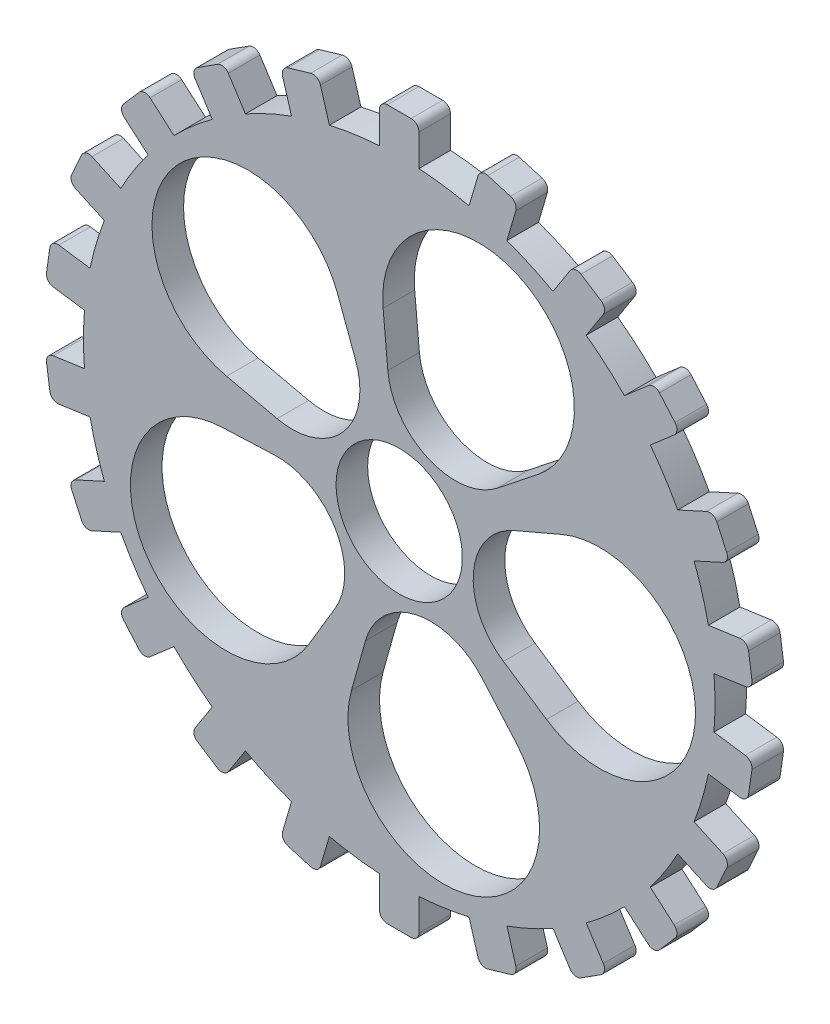
SolidWorks part; units mm, degrees
ref_plane "Front Plane" through (0, 0, 0) normal (0, 0, 1) x (1, 0, 0)
ref_plane "Top Plane" through (0, 0, 0) normal (0, 1, 0) x (1, 0, 0)
ref_plane "Right Plane" through (0, 0, 0) normal (1, 0, 0) x (0, 0, -1)
sketch "Sketch1" plane through (0, 0, 0) normal (0, 0, 1) x (1, 0, 0)
  line L0 (22.4753, 99.0829) -> (25.3377, 108.8314)
  line L2 (-6.35, 101.4014) -> (-6.35, 111.5614)
  line L3 (-3.81, 114.1014) -> (3.81, 114.1014)
  line L4 (6.35, 101.4014) -> (6.35, 111.5614)
  line L5 (28.4904, 110.5529) -> (35.8017, 108.4061)
  line L6 (34.6608, 95.5049) -> (37.5232, 105.2533)
  line L8 (49.4798, 88.7373) -> (54.9727, 97.2845)
  line L9 (58.4827, 98.048) -> (64.893, 93.9283)
  line L10 (60.1637, 81.8712) -> (65.6566, 90.4183)
  line L12 (72.4757, 71.2028) -> (80.1541, 77.8562)
  line L13 (83.737, 77.5999) -> (88.7271, 71.8411)
  line L14 (80.7924, 61.6048) -> (88.4708, 68.2581)
  line L16 (89.6, 47.8998) -> (98.8419, 52.1204)
  line L17 (102.2075, 50.8651) -> (105.373, 43.9337)
  line L18 (94.8758, 36.3475) -> (104.1177, 40.5681)
  line L20 (99.4655, 20.7163) -> (109.5221, 22.1622)
  line L21 (112.3978, 20.0095) -> (113.4822, 12.4671)
  line L22 (101.2729, 8.1456) -> (111.3295, 9.5915)
  line L24 (101.2729, -8.1456) -> (111.3295, -9.5915)
  line L25 (113.4822, -12.4671) -> (112.3978, -20.0095)
  line L26 (99.4655, -20.7163) -> (109.5221, -22.1622)
  line L28 (94.8758, -36.3475) -> (104.1177, -40.5681)
  line L29 (105.373, -43.9337) -> (102.2075, -50.8651)
  line L30 (89.6, -47.8998) -> (98.8419, -52.1204)
  line L32 (80.7924, -61.6048) -> (88.4708, -68.2581)
  line L33 (88.7271, -71.8411) -> (83.737, -77.5999)
  line L34 (72.4757, -71.2028) -> (80.1541, -77.8562)
  line L36 (60.1637, -81.8712) -> (65.6566, -90.4183)
  line L37 (64.893, -93.9283) -> (58.4827, -98.048)
  line L38 (49.4798, -88.7373) -> (54.9727, -97.2845)
  line L40 (34.6608, -95.5049) -> (37.5232, -105.2533)
  line L41 (35.8017, -108.4061) -> (28.4904, -110.5529)
  line L42 (22.4753, -99.0829) -> (25.3377, -108.8314)
  line L44 (6.35, -101.4014) -> (6.35, -111.5614)
  line L45 (3.81, -114.1014) -> (-3.81, -114.1014)
  line L46 (-6.35, -101.4014) -> (-6.35, -111.5614)
  line L48 (-22.4753, -99.0829) -> (-25.3377, -108.8314)
  line L49 (-28.4904, -110.5529) -> (-35.8017, -108.4061)
  line L50 (-34.6608, -95.5049) -> (-37.5232, -105.2533)
  line L52 (-49.4798, -88.7373) -> (-54.9727, -97.2845)
  line L53 (-58.4827, -98.048) -> (-64.893, -93.9283)
  line L54 (-60.1637, -81.8712) -> (-65.6566, -90.4183)
  line L56 (-72.4757, -71.2028) -> (-80.1541, -77.8562)
  line L57 (-83.737, -77.5999) -> (-88.7271, -71.8411)
  line L58 (-80.7924, -61.6048) -> (-88.4708, -68.2581)
  line L60 (-89.6, -47.8998) -> (-98.8419, -52.1204)
  line L61 (-102.2075, -50.8651) -> (-105.373, -43.9337)
  line L62 (-94.8758, -36.3475) -> (-104.1177, -40.5681)
  line L64 (-99.4655, -20.7163) -> (-109.5221, -22.1622)
  line L65 (-112.3978, -20.0095) -> (-113.4822, -12.4671)
  line L66 (-101.2729, -8.1456) -> (-111.3295, -9.5915)
  line L68 (-101.2729, 8.1456) -> (-111.3295, 9.5915)
  line L69 (-113.4822, 12.4671) -> (-112.3978, 20.0095)
  line L70 (-99.4655, 20.7163) -> (-109.5221, 22.1622)
  line L72 (-94.8758, 36.3475) -> (-104.1177, 40.5681)
  line L73 (-105.373, 43.9337) -> (-102.2075, 50.8651)
  line L74 (-89.6, 47.8998) -> (-98.8419, 52.1204)
  line L76 (-80.7924, 61.6048) -> (-88.4708, 68.2581)
  line L77 (-88.7271, 71.8411) -> (-83.737, 77.5999)
  line L78 (-72.4757, 71.2028) -> (-80.1541, 77.8562)
  line L80 (-60.1637, 81.8712) -> (-65.6566, 90.4183)
  line L81 (-64.893, 93.9283) -> (-58.4827, 98.048)
  line L82 (-49.4798, 88.7373) -> (-54.9727, 97.2845)
  line L84 (-34.6608, 95.5049) -> (-37.5232, 105.2533)
  line L85 (-35.8017, 108.4061) -> (-28.4904, 110.5529)
  line L86 (-22.4753, 99.0829) -> (-25.3377, 108.8314)
  arc A0 (-34.6608, 95.5049) -> (-49.4798, 88.7373) centre (0, 0) ccw
  arc A2 (-6.35, 101.4014) -> (-22.4753, 99.0829) centre (0, 0) ccw
  arc A3 (22.4753, 99.0829) -> (6.35, 101.4014) centre (0, 0) ccw
  arc A4 (49.4798, 88.7373) -> (34.6608, 95.5049) centre (0, 0) ccw
  arc A5 (72.4757, 71.2028) -> (60.1637, 81.8712) centre (0, 0) ccw
  arc A6 (89.6, 47.8998) -> (80.7924, 61.6048) centre (0, 0) ccw
  arc A7 (99.4655, 20.7163) -> (94.8758, 36.3475) centre (0, 0) ccw
  arc A8 (101.2729, -8.1456) -> (101.2729, 8.1456) centre (0, 0) ccw
  arc A9 (94.8758, -36.3475) -> (99.4655, -20.7163) centre (0, 0) ccw
  arc A10 (80.7924, -61.6048) -> (89.6, -47.8998) centre (0, 0) ccw
  arc A11 (60.1637, -81.8712) -> (72.4757, -71.2028) centre (0, 0) ccw
  arc A12 (34.6608, -95.5049) -> (49.4798, -88.7373) centre (0, 0) ccw
  arc A13 (-22.4753, -99.0829) -> (-6.35, -101.4014) centre (0, 0) ccw
  arc A14 (6.35, -101.4014) -> (22.4753, -99.0829) centre (0, 0) ccw
  arc A15 (-60.1637, 81.8712) -> (-72.4757, 71.2028) centre (0, 0) ccw
  arc A16 (-80.7924, 61.6048) -> (-89.6, 47.8998) centre (0, 0) ccw
  arc A17 (-94.8758, 36.3475) -> (-99.4655, 20.7163) centre (0, 0) ccw
  arc A18 (-101.2729, 8.1456) -> (-101.2729, -8.1456) centre (0, 0) ccw
  arc A19 (-99.4655, -20.7163) -> (-94.8758, -36.3475) centre (0, 0) ccw
  arc A20 (-89.6, -47.8998) -> (-80.7924, -61.6048) centre (0, 0) ccw
  arc A21 (-72.4757, -71.2028) -> (-60.1637, -81.8712) centre (0, 0) ccw
  arc A22 (-49.4798, -88.7373) -> (-34.6608, -95.5049) centre (0, 0) ccw
  arc A23 (102.2075, 50.8651) -> (98.8419, 52.1204) centre (99.8971, 49.81) ccw
  arc A24 (83.737, 77.5999) -> (80.1541, 77.8562) centre (81.8174, 75.9366) ccw
  arc A25 (58.4827, 98.048) -> (54.9727, 97.2845) centre (57.1095, 95.9112) ccw
  arc A26 (28.4904, 110.5529) -> (25.3377, 108.8314) centre (27.7748, 108.1158) ccw
  arc A27 (-3.81, 114.1014) -> (-6.35, 111.5614) centre (-3.81, 111.5614) ccw
  arc A28 (-25.3377, 108.8314) -> (-28.4904, 110.5529) centre (-27.7748, 108.1158) ccw
  arc A29 (-35.8017, 108.4061) -> (-37.5232, 105.2533) centre (-35.0861, 105.9689) ccw
  arc A30 (-54.9727, 97.2845) -> (-58.4827, 98.048) centre (-57.1095, 95.9112) ccw
  arc A31 (-64.893, 93.9283) -> (-65.6566, 90.4183) centre (-63.5198, 91.7916) ccw
  arc A32 (-83.737, 77.5999) -> (-80.1541, 77.8562) centre (-81.8174, 75.9366) cw
  arc A33 (-88.7271, 71.8411) -> (-88.4708, 68.2581) centre (-86.8075, 70.1778) ccw
  arc A34 (-98.8419, 52.1204) -> (-102.2075, 50.8651) centre (-99.8971, 49.81) ccw
  arc A35 (-105.373, 43.9337) -> (-104.1177, 40.5681) centre (-103.0625, 42.8786) ccw
  arc A36 (-109.5221, 22.1622) -> (-112.3978, 20.0095) centre (-109.8836, 19.6481) ccw
  arc A37 (-113.4822, 12.4671) -> (-111.3295, 9.5915) centre (-110.9681, 12.1056) ccw
  arc A38 (-111.3295, -9.5915) -> (-113.4822, -12.4671) centre (-110.9681, -12.1056) ccw
  arc A39 (-109.5221, -22.1622) -> (-112.3978, -20.0095) centre (-109.8836, -19.6481) cw
  arc A40 (-104.1177, -40.5681) -> (-105.373, -43.9337) centre (-103.0625, -42.8786) ccw
  arc A41 (-102.2075, -50.8651) -> (-98.8419, -52.1204) centre (-99.8971, -49.81) ccw
  arc A42 (-88.4708, -68.2581) -> (-88.7271, -71.8411) centre (-86.8075, -70.1778) ccw
  arc A43 (-83.737, -77.5999) -> (-80.1541, -77.8562) centre (-81.8174, -75.9366) ccw
  arc A44 (-65.6566, -90.4183) -> (-64.893, -93.9283) centre (-63.5198, -91.7916) ccw
  arc A45 (-58.4827, -98.048) -> (-54.9727, -97.2845) centre (-57.1095, -95.9112) ccw
  arc A46 (-37.5232, -105.2533) -> (-35.8017, -108.4061) centre (-35.0861, -105.9689) ccw
  arc A47 (-28.4904, -110.5529) -> (-25.3377, -108.8314) centre (-27.7748, -108.1158) ccw
  arc A48 (-6.35, -111.5614) -> (-3.81, -114.1014) centre (-3.81, -111.5614) ccw
  arc A49 (3.81, -114.1014) -> (6.35, -111.5614) centre (3.81, -111.5614) ccw
  arc A50 (25.3377, -108.8314) -> (28.4904, -110.5529) centre (27.7748, -108.1158) ccw
  arc A51 (35.8017, -108.4061) -> (37.5232, -105.2533) centre (35.0861, -105.9689) ccw
  arc A52 (54.9727, -97.2845) -> (58.4827, -98.048) centre (57.1095, -95.9112) ccw
  arc A53 (64.893, -93.9283) -> (65.6566, -90.4183) centre (63.5198, -91.7916) ccw
  arc A54 (80.1541, -77.8562) -> (83.737, -77.5999) centre (81.8174, -75.9366) ccw
  arc A55 (88.7271, -71.8411) -> (88.4708, -68.2581) centre (86.8075, -70.1778) ccw
  arc A56 (98.8419, -52.1204) -> (102.2075, -50.8651) centre (99.8971, -49.81) ccw
  arc A57 (105.373, -43.9337) -> (104.1177, -40.5681) centre (103.0625, -42.8786) ccw
  arc A58 (109.5221, -22.1622) -> (112.3978, -20.0095) centre (109.8836, -19.6481) ccw
  arc A59 (113.4822, -12.4671) -> (111.3295, -9.5915) centre (110.9681, -12.1056) ccw
  arc A60 (113.4822, 12.4671) -> (111.3295, 9.5915) centre (110.9681, 12.1056) cw
  arc A61 (112.3978, 20.0095) -> (109.5221, 22.1622) centre (109.8836, 19.6481) ccw
  arc A62 (105.373, 43.9337) -> (104.1177, 40.5681) centre (103.0625, 42.8786) cw
  arc A63 (88.7271, 71.8411) -> (88.4708, 68.2581) centre (86.8075, 70.1778) cw
  arc A64 (65.6566, 90.4183) -> (64.893, 93.9283) centre (63.5198, 91.7916) ccw
  arc A65 (35.8017, 108.4061) -> (37.5232, 105.2533) centre (35.0861, 105.9689) cw
  arc A66 (3.81, 114.1014) -> (6.35, 111.5614) centre (3.81, 111.5614) cw
  point P94 (0, 0)
  point P102 (-6.35, 114.1014)
  point P181 (6.35, 114.1014)
  dimension "D1" = 203.2
  dimension "D6" = 2.54
  dimension "D2" = 12.7
  dimension "D3" = 12.7
  dimension "D4" = 22
extrude "Boss-Extrude1" add sketch "Sketch1" along normal blind 10.16 contours A3 L4 A66 L3 A27 L2 A2 L86 A28 L85 A29 L84 A0 L82 A30 L81 A31 L80 A15 L78 A32 L77 A33 L76 A16 L74 A34 L73 A35 L72 A17 L70 A36 L69 A37 L68 A18 L66 A38 L65 A39 L64 A19 L62 A40 L61 A41 L60 A20 L58 A42 L57 A43 L56 A21 L54 A44 L53 A45 L52 A22 L50 A46 L49 A47 L48 A13 L46 A48 L45 A49 L44 A14 L42 A50 L41 A51 L40 A12 L38 A52 L37 A53 L36 A11 L34 A54 L33 A55 L32 A10 L30 A56 L29 A57 L28 A9 L26 A58 L25 A59 L24 A8 L22 A60 L21 A61 L20 A7 L18 A62 L17 A23 L16 A6 L14 A63 L13 A24 L12 A5 L10 A64 L9 A25 L8 A4 L6 A65 L5 A26 L0
sketch "Sketch5" plane through (0, 0, 0) normal (0, 0, -1) x (-1, 0, 0)
  circle A0 centre (0, 0) radius 20.32
extrude "Cut-Extrude1" cut sketch "Sketch5" against normal blind 10.16
sketch "Sketch7" plane through (0, 0, 0) normal (0, 0, -1) x (-1, 0, 0)
  line L0 (56.9012, -2.3358) -> (40.2429, -1.652)
  line L1 (20.6116, -34.6033) -> (29.1436, -48.927)
  line L2 (19.8049, 53.3944) -> (14.0069, 37.7628)
  line L3 (39.279, 8.9098) -> (55.5382, 12.5979)
  line L4 (15.3619, -54.838) -> (10.8646, -38.7838)
  line L5 (-26.5403, -30.2958) -> (-37.5265, -42.8365)
  line L6 (-47.407, -31.556) -> (-33.5282, -22.3177)
  line L7 (-37.0144, 15.8794) -> (-52.3362, 22.4526)
  line L8 (-44.6611, 35.3354) -> (-31.5862, 24.9907)
  line L9 (3.6642, 40.1098) -> (5.1809, 56.7129)
  arc A1 (55.5382, 12.5979) -> (19.8049, 53.3944) centre (48.7167, 42.6705) ccw
  arc A2 (14.0069, 37.7628) -> (39.279, 8.9098) centre (34.4545, 30.1784) ccw
  arc A3 (40.2429, -1.652) -> (20.6116, -34.6033) centre (39.3484, -23.4426) ccw
  arc A4 (29.1436, -48.927) -> (56.9012, -2.3358) centre (55.6364, -33.1465) ccw
  arc A5 (10.8646, -38.7838) -> (-26.5403, -30.2958) centre (-10.1359, -44.6667) ccw
  arc A6 (-37.5265, -42.8365) -> (15.3619, -54.838) centre (-14.3316, -63.1562) ccw
  arc A7 (-33.5282, -22.3177) -> (-37.0144, 15.8794) centre (-45.6127, -4.163) ccw
  arc A8 (-52.3362, 22.4526) -> (-47.407, -31.556) centre (-64.4938, -5.8862) ccw
  arc A9 (-31.5862, 24.9907) -> (3.6642, 40.1098) centre (-18.0543, 42.0939) ccw
  arc A10 (5.1809, 56.7129) -> (-44.6611, 35.3354) centre (-25.5278, 59.5183) ccw
  point P17 (0, 0)
  point P36 (0, 0)
  dimension "D1" = 5
extrude "Cut-Extrude2" cut sketch "Sketch7" against normal blind 10.16
